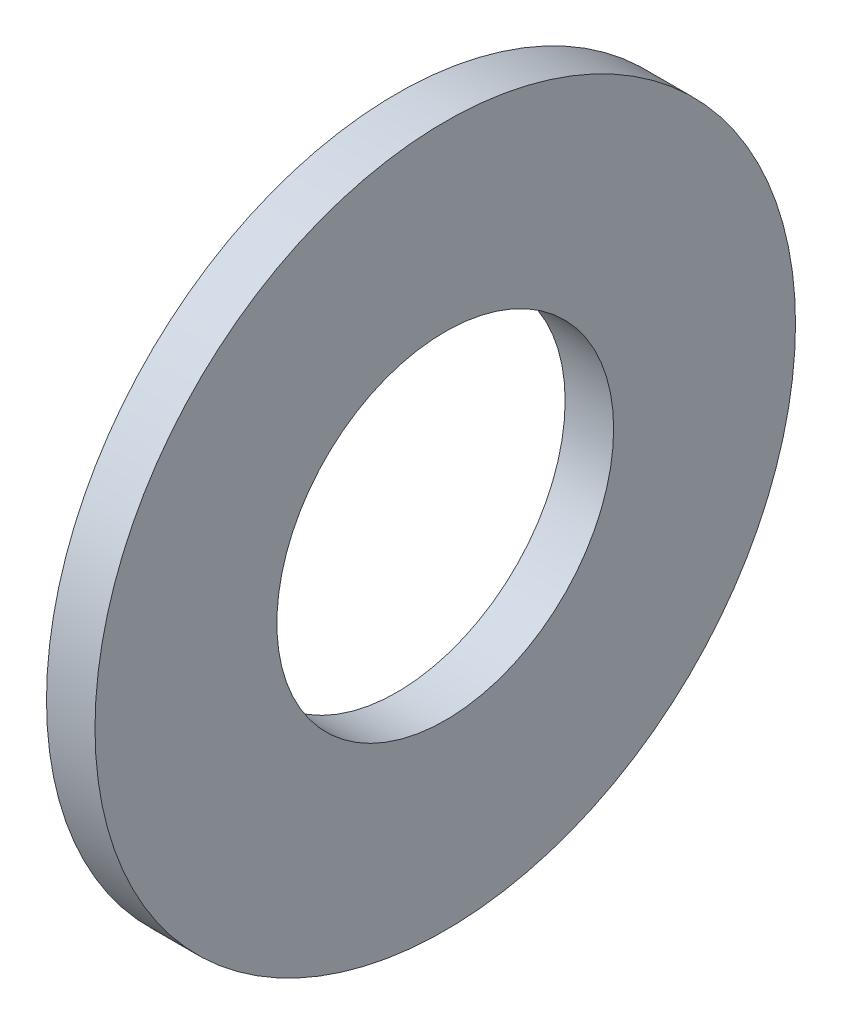
SolidWorks part; units mm, degrees
ref_plane "Front Plane" through (0, 0, 0) normal (0, 0, 1) x (1, 0, 0)
ref_plane "Top Plane" through (0, 0, 0) normal (0, 1, 0) x (1, 0, 0)
ref_plane "Right Plane" through (0, 0, 0) normal (1, 0, 0) x (0, 0, -1)
sketch "Sketch1" plane through (0, 0, 0) normal (1, 0, 0) x (0, 0, -1)
  circle A0 centre (0, 0) radius 26
  circle A1 centre (0, 0) radius 12.5
  dimension "D1" = 52
  dimension "D2" = 25
extrude "Boss-Extrude1" add sketch "Sketch1" along normal blind 3.6
